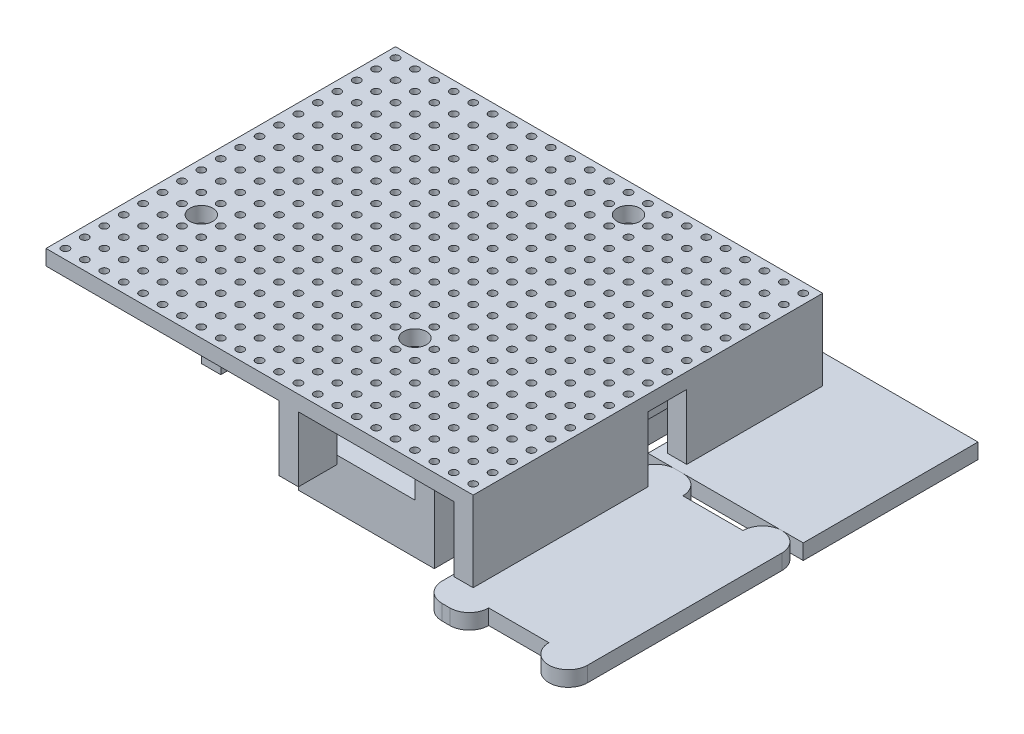
SolidWorks part; units mm, degrees
ref_plane "Front Plane" through (0, 0, 0) normal (0, 0, 1) x (1, 0, 0)
ref_plane "Top Plane" through (0, 0, 0) normal (0, 1, 0) x (1, 0, 0)
ref_plane "Right Plane" through (0, 0, 0) normal (1, 0, 0) x (0, 0, -1)
sketch "Sketch1" plane through (0, 0, 0) normal (0, 1, 0) x (1, 0, 0)
  line L1 (-28.6326, 15.7481) -> (34.8674, 15.7481)
  line L2 (-28.6326, 15.7481) -> (-28.6326, -29.9719)
  line L3 (-28.6326, -29.9719) -> (34.8674, -29.9719)
  line L4 (34.8674, 15.7481) -> (34.8674, -29.9719)
  circle A0 centre (33.5974, -28.7019) radius 0.5
  circle A1 centre (31.0574, -28.7019) radius 0.5
  circle A2 centre (28.5174, -28.7019) radius 0.5
  circle A3 centre (25.9774, -28.7019) radius 0.5
  circle A4 centre (23.4374, -28.7019) radius 0.5
  circle A5 centre (20.8974, -28.7019) radius 0.5
  circle A6 centre (18.3574, -28.7019) radius 0.5
  circle A7 centre (15.8174, -28.7019) radius 0.5
  circle A8 centre (13.2774, -28.7019) radius 0.5
  circle A9 centre (10.7374, -28.7019) radius 0.5
  circle A10 centre (8.1974, -28.7019) radius 0.5
  circle A11 centre (5.6574, -28.7019) radius 0.5
  circle A12 centre (3.1174, -28.7019) radius 0.5
  circle A13 centre (0.5774, -28.7019) radius 0.5
  circle A14 centre (-1.9626, -28.7019) radius 0.5
  circle A15 centre (-4.5026, -28.7019) radius 0.5
  circle A16 centre (-7.0426, -28.7019) radius 0.5
  circle A17 centre (-9.5826, -28.7019) radius 0.5
  circle A18 centre (-12.1226, -28.7019) radius 0.5
  circle A19 centre (-14.6626, -28.7019) radius 0.5
  circle A20 centre (-17.2026, -28.7019) radius 0.5
  circle A21 centre (-19.7426, -28.7019) radius 0.5
  circle A22 centre (-22.2826, -28.7019) radius 0.5
  circle A23 centre (-24.8226, -28.7019) radius 0.5
  circle A24 centre (-27.3626, -28.7019) radius 0.5
  circle A25 centre (31.0574, -26.1619) radius 0.5
  circle A26 centre (28.5174, -26.1619) radius 0.5
  circle A27 centre (25.9774, -26.1619) radius 0.5
  circle A28 centre (23.4374, -26.1619) radius 0.5
  circle A29 centre (20.8974, -26.1619) radius 0.5
  circle A30 centre (18.3574, -26.1619) radius 0.5
  circle A31 centre (15.8174, -26.1619) radius 0.5
  circle A32 centre (13.2774, -26.1619) radius 0.5
  circle A33 centre (10.7374, -26.1619) radius 0.5
  circle A34 centre (8.1974, -26.1619) radius 0.5
  circle A35 centre (5.6574, -26.1619) radius 0.5
  circle A36 centre (3.1174, -26.1619) radius 0.5
  circle A37 centre (0.5774, -26.1619) radius 0.5
  circle A38 centre (-1.9626, -26.1619) radius 0.5
  circle A39 centre (-4.5026, -26.1619) radius 0.5
  circle A40 centre (-7.0426, -26.1619) radius 0.5
  circle A41 centre (-9.5826, -26.1619) radius 0.5
  circle A42 centre (-12.1226, -26.1619) radius 0.5
  circle A43 centre (-14.6626, -26.1619) radius 0.5
  circle A44 centre (-17.2026, -26.1619) radius 0.5
  circle A45 centre (-19.7426, -26.1619) radius 0.5
  circle A46 centre (-22.2826, -26.1619) radius 0.5
  circle A47 centre (-24.8226, -26.1619) radius 0.5
  circle A48 centre (-27.3626, -26.1619) radius 0.5
  circle A49 centre (31.0574, -23.6219) radius 0.5
  circle A50 centre (28.5174, -23.6219) radius 0.5
  circle A51 centre (25.9774, -23.6219) radius 0.5
  circle A52 centre (23.4374, -23.6219) radius 0.5
  circle A53 centre (20.8974, -23.6219) radius 0.5
  circle A54 centre (18.3574, -23.6219) radius 0.5
  circle A55 centre (15.8174, -23.6219) radius 0.5
  circle A56 centre (13.2774, -23.6219) radius 0.5
  circle A57 centre (10.7374, -23.6219) radius 0.5
  circle A58 centre (8.1974, -23.6219) radius 0.5
  circle A59 centre (5.6574, -23.6219) radius 0.5
  circle A60 centre (3.1174, -23.6219) radius 0.5
  circle A61 centre (0.5774, -23.6219) radius 0.5
  circle A62 centre (-1.9626, -23.6219) radius 0.5
  circle A63 centre (-4.5026, -23.6219) radius 0.5
  circle A64 centre (-7.0426, -23.6219) radius 0.5
  circle A65 centre (-9.5826, -23.6219) radius 0.5
  circle A66 centre (-12.1226, -23.6219) radius 0.5
  circle A67 centre (-14.6626, -23.6219) radius 0.5
  circle A68 centre (-17.2026, -23.6219) radius 0.5
  circle A69 centre (-19.7426, -23.6219) radius 0.5
  circle A70 centre (-22.2826, -23.6219) radius 0.5
  circle A71 centre (-24.8226, -23.6219) radius 0.5
  circle A72 centre (-27.3626, -23.6219) radius 0.5
  circle A73 centre (31.0574, -21.0819) radius 0.5
  circle A74 centre (28.5174, -21.0819) radius 0.5
  circle A75 centre (25.9774, -21.0819) radius 0.5
  circle A76 centre (23.4374, -21.0819) radius 0.5
  circle A77 centre (20.8974, -21.0819) radius 0.5
  circle A78 centre (18.3574, -21.0819) radius 0.5
  circle A79 centre (15.8174, -21.0819) radius 0.5
  circle A80 centre (13.2774, -21.0819) radius 0.5
  circle A81 centre (10.7374, -21.0819) radius 0.5
  circle A82 centre (8.1974, -21.0819) radius 0.5
  circle A83 centre (5.6574, -21.0819) radius 0.5
  circle A84 centre (3.1174, -21.0819) radius 0.5
  circle A85 centre (0.5774, -21.0819) radius 0.5
  circle A86 centre (-1.9626, -21.0819) radius 0.5
  circle A87 centre (-4.5026, -21.0819) radius 0.5
  circle A88 centre (-7.0426, -21.0819) radius 0.5
  circle A89 centre (-9.5826, -21.0819) radius 0.5
  circle A90 centre (-12.1226, -21.0819) radius 0.5
  circle A91 centre (-14.6626, -21.0819) radius 0.5
  circle A92 centre (-17.2026, -21.0819) radius 0.5
  circle A93 centre (-19.7426, -21.0819) radius 0.5
  circle A94 centre (-22.2826, -21.0819) radius 0.5
  circle A95 centre (-24.8226, -21.0819) radius 0.5
  circle A96 centre (-27.3626, -21.0819) radius 0.5
  circle A97 centre (31.0574, -18.5419) radius 0.5
  circle A98 centre (28.5174, -18.5419) radius 0.5
  circle A99 centre (25.9774, -18.5419) radius 0.5
  circle A100 centre (23.4374, -18.5419) radius 0.5
  circle A101 centre (20.8974, -18.5419) radius 0.5
  circle A102 centre (18.3574, -18.5419) radius 0.5
  circle A103 centre (15.8174, -18.5419) radius 0.5
  circle A104 centre (13.2774, -18.5419) radius 0.5
  circle A105 centre (10.7374, -18.5419) radius 0.5
  circle A106 centre (8.1974, -18.5419) radius 0.5
  circle A107 centre (5.6574, -18.5419) radius 0.5
  circle A108 centre (3.1174, -18.5419) radius 0.5
  circle A109 centre (0.5774, -18.5419) radius 0.5
  circle A110 centre (-1.9626, -18.5419) radius 0.5
  circle A111 centre (-4.5026, -18.5419) radius 0.5
  circle A112 centre (-7.0426, -18.5419) radius 0.5
  circle A113 centre (-9.5826, -18.5419) radius 0.5
  circle A114 centre (-12.1226, -18.5419) radius 0.5
  circle A115 centre (-14.6626, -18.5419) radius 0.5
  circle A116 centre (-17.2026, -18.5419) radius 0.5
  circle A117 centre (-19.7426, -18.5419) radius 0.5
  circle A118 centre (-22.2826, -18.5419) radius 0.5
  circle A119 centre (-24.8226, -18.5419) radius 0.5
  circle A120 centre (-27.3626, -18.5419) radius 0.5
  circle A121 centre (31.0574, -16.0019) radius 0.5
  circle A122 centre (28.5174, -16.0019) radius 0.5
  circle A123 centre (25.9774, -16.0019) radius 0.5
  circle A124 centre (23.4374, -16.0019) radius 0.5
  circle A125 centre (20.8974, -16.0019) radius 0.5
  circle A126 centre (18.3574, -16.0019) radius 0.5
  circle A127 centre (15.8174, -16.0019) radius 0.5
  circle A128 centre (13.2774, -16.0019) radius 0.5
  circle A129 centre (10.7374, -16.0019) radius 0.5
  circle A130 centre (8.1974, -16.0019) radius 0.5
  circle A131 centre (5.6574, -16.0019) radius 0.5
  circle A132 centre (3.1174, -16.0019) radius 0.5
  circle A133 centre (0.5774, -16.0019) radius 0.5
  circle A134 centre (-1.9626, -16.0019) radius 0.5
  circle A135 centre (-4.5026, -16.0019) radius 0.5
  circle A136 centre (-7.0426, -16.0019) radius 0.5
  circle A137 centre (-9.5826, -16.0019) radius 0.5
  circle A138 centre (-12.1226, -16.0019) radius 0.5
  circle A139 centre (-14.6626, -16.0019) radius 0.5
  circle A140 centre (-17.2026, -16.0019) radius 0.5
  circle A141 centre (-19.7426, -16.0019) radius 0.5
  circle A142 centre (-22.2826, -16.0019) radius 0.5
  circle A143 centre (-24.8226, -16.0019) radius 0.5
  circle A144 centre (-27.3626, -16.0019) radius 0.5
  circle A145 centre (31.0574, -13.4619) radius 0.5
  circle A146 centre (28.5174, -13.4619) radius 0.5
  circle A147 centre (25.9774, -13.4619) radius 0.5
  circle A148 centre (23.4374, -13.4619) radius 0.5
  circle A149 centre (20.8974, -13.4619) radius 0.5
  circle A150 centre (18.3574, -13.4619) radius 0.5
  circle A151 centre (15.8174, -13.4619) radius 0.5
  circle A152 centre (13.2774, -13.4619) radius 0.5
  circle A153 centre (10.7374, -13.4619) radius 0.5
  circle A154 centre (8.1974, -13.4619) radius 0.5
  circle A155 centre (5.6574, -13.4619) radius 0.5
  circle A156 centre (3.1174, -13.4619) radius 0.5
  circle A157 centre (0.5774, -13.4619) radius 0.5
  circle A158 centre (-1.9626, -13.4619) radius 0.5
  circle A159 centre (-4.5026, -13.4619) radius 0.5
  circle A160 centre (-7.0426, -13.4619) radius 0.5
  circle A161 centre (-9.5826, -13.4619) radius 0.5
  circle A162 centre (-12.1226, -13.4619) radius 0.5
  circle A163 centre (-14.6626, -13.4619) radius 0.5
  circle A164 centre (-17.2026, -13.4619) radius 0.5
  circle A165 centre (-19.7426, -13.4619) radius 0.5
  circle A166 centre (-22.2826, -13.4619) radius 0.5
  circle A167 centre (-24.8226, -13.4619) radius 0.5
  circle A168 centre (-27.3626, -13.4619) radius 0.5
  circle A169 centre (31.0574, -10.9219) radius 0.5
  circle A170 centre (28.5174, -10.9219) radius 0.5
  circle A171 centre (25.9774, -10.9219) radius 0.5
  circle A172 centre (23.4374, -10.9219) radius 0.5
  circle A173 centre (20.8974, -10.9219) radius 0.5
  circle A174 centre (18.3574, -10.9219) radius 0.5
  circle A175 centre (15.8174, -10.9219) radius 0.5
  circle A176 centre (13.2774, -10.9219) radius 0.5
  circle A177 centre (10.7374, -10.9219) radius 0.5
  circle A178 centre (8.1974, -10.9219) radius 0.5
  circle A179 centre (5.6574, -10.9219) radius 0.5
  circle A180 centre (3.1174, -10.9219) radius 0.5
  circle A181 centre (0.5774, -10.9219) radius 0.5
  circle A182 centre (-1.9626, -10.9219) radius 0.5
  circle A183 centre (-4.5026, -10.9219) radius 0.5
  circle A184 centre (-7.0426, -10.9219) radius 0.5
  circle A185 centre (-9.5826, -10.9219) radius 0.5
  circle A186 centre (-12.1226, -10.9219) radius 0.5
  circle A187 centre (-14.6626, -10.9219) radius 0.5
  circle A188 centre (-17.2026, -10.9219) radius 0.5
  circle A189 centre (-19.7426, -10.9219) radius 0.5
  circle A190 centre (-22.2826, -10.9219) radius 0.5
  circle A191 centre (-24.8226, -10.9219) radius 0.5
  circle A192 centre (-27.3626, -10.9219) radius 0.5
  circle A193 centre (31.0574, -8.3819) radius 0.5
  circle A194 centre (28.5174, -8.3819) radius 0.5
  circle A195 centre (25.9774, -8.3819) radius 0.5
  circle A196 centre (23.4374, -8.3819) radius 0.5
  circle A197 centre (20.8974, -8.3819) radius 0.5
  circle A198 centre (18.3574, -8.3819) radius 0.5
  circle A199 centre (15.8174, -8.3819) radius 0.5
  circle A200 centre (13.2774, -8.3819) radius 0.5
  circle A201 centre (10.7374, -8.3819) radius 0.5
  circle A202 centre (8.1974, -8.3819) radius 0.5
  circle A203 centre (5.6574, -8.3819) radius 0.5
  circle A204 centre (3.1174, -8.3819) radius 0.5
  circle A205 centre (0.5774, -8.3819) radius 0.5
  circle A206 centre (-1.9626, -8.3819) radius 0.5
  circle A207 centre (-4.5026, -8.3819) radius 0.5
  circle A208 centre (-7.0426, -8.3819) radius 0.5
  circle A209 centre (-9.5826, -8.3819) radius 0.5
  circle A210 centre (-12.1226, -8.3819) radius 0.5
  circle A211 centre (-14.6626, -8.3819) radius 0.5
  circle A212 centre (-17.2026, -8.3819) radius 0.5
  circle A213 centre (-19.7426, -8.3819) radius 0.5
  circle A214 centre (-22.2826, -8.3819) radius 0.5
  circle A215 centre (-24.8226, -8.3819) radius 0.5
  circle A216 centre (-27.3626, -8.3819) radius 0.5
  circle A217 centre (31.0574, -5.8419) radius 0.5
  circle A218 centre (28.5174, -5.8419) radius 0.5
  circle A219 centre (25.9774, -5.8419) radius 0.5
  circle A220 centre (23.4374, -5.8419) radius 0.5
  circle A221 centre (20.8974, -5.8419) radius 0.5
  circle A222 centre (18.3574, -5.8419) radius 0.5
  circle A223 centre (15.8174, -5.8419) radius 0.5
  circle A224 centre (13.2774, -5.8419) radius 0.5
  circle A225 centre (10.7374, -5.8419) radius 0.5
  circle A226 centre (8.1974, -5.8419) radius 0.5
  circle A227 centre (5.6574, -5.8419) radius 0.5
  circle A228 centre (3.1174, -5.8419) radius 0.5
  circle A229 centre (0.5774, -5.8419) radius 0.5
  circle A230 centre (-1.9626, -5.8419) radius 0.5
  circle A231 centre (-4.5026, -5.8419) radius 0.5
  circle A232 centre (-7.0426, -5.8419) radius 0.5
  circle A233 centre (-9.5826, -5.8419) radius 0.5
  circle A234 centre (-12.1226, -5.8419) radius 0.5
  circle A235 centre (-14.6626, -5.8419) radius 0.5
  circle A236 centre (-17.2026, -5.8419) radius 0.5
  circle A237 centre (-19.7426, -5.8419) radius 0.5
  circle A238 centre (-22.2826, -5.8419) radius 0.5
  circle A239 centre (-24.8226, -5.8419) radius 0.5
  circle A240 centre (-27.3626, -5.8419) radius 0.5
  circle A241 centre (31.0574, -3.3019) radius 0.5
  circle A242 centre (28.5174, -3.3019) radius 0.5
  circle A243 centre (25.9774, -3.3019) radius 0.5
  circle A244 centre (23.4374, -3.3019) radius 0.5
  circle A245 centre (20.8974, -3.3019) radius 0.5
  circle A246 centre (18.3574, -3.3019) radius 0.5
  circle A247 centre (15.8174, -3.3019) radius 0.5
  circle A248 centre (13.2774, -3.3019) radius 0.5
  circle A249 centre (10.7374, -3.3019) radius 0.5
  circle A250 centre (8.1974, -3.3019) radius 0.5
  circle A251 centre (5.6574, -3.3019) radius 0.5
  circle A252 centre (3.1174, -3.3019) radius 0.5
  circle A253 centre (0.5774, -3.3019) radius 0.5
  circle A254 centre (-1.9626, -3.3019) radius 0.5
  circle A255 centre (-4.5026, -3.3019) radius 0.5
  circle A256 centre (-7.0426, -3.3019) radius 0.5
  circle A257 centre (-9.5826, -3.3019) radius 0.5
  circle A258 centre (-12.1226, -3.3019) radius 0.5
  circle A259 centre (-14.6626, -3.3019) radius 0.5
  circle A260 centre (-17.2026, -3.3019) radius 0.5
  circle A261 centre (-19.7426, -3.3019) radius 0.5
  circle A262 centre (-22.2826, -3.3019) radius 0.5
  circle A263 centre (-24.8226, -3.3019) radius 0.5
  circle A264 centre (-27.3626, -3.3019) radius 0.5
  circle A265 centre (31.0574, -0.7619) radius 0.5
  circle A266 centre (28.5174, -0.7619) radius 0.5
  circle A267 centre (25.9774, -0.7619) radius 0.5
  circle A268 centre (23.4374, -0.7619) radius 0.5
  circle A269 centre (20.8974, -0.7619) radius 0.5
  circle A270 centre (18.3574, -0.7619) radius 0.5
  circle A271 centre (15.8174, -0.7619) radius 0.5
  circle A272 centre (13.2774, -0.7619) radius 0.5
  circle A273 centre (10.7374, -0.7619) radius 0.5
  circle A274 centre (8.1974, -0.7619) radius 0.5
  circle A275 centre (5.6574, -0.7619) radius 0.5
  circle A276 centre (3.1174, -0.7619) radius 0.5
  circle A277 centre (0.5774, -0.7619) radius 0.5
  circle A278 centre (-1.9626, -0.7619) radius 0.5
  circle A279 centre (-4.5026, -0.7619) radius 0.5
  circle A280 centre (-7.0426, -0.7619) radius 0.5
  circle A281 centre (-9.5826, -0.7619) radius 0.5
  circle A282 centre (-12.1226, -0.7619) radius 0.5
  circle A283 centre (-14.6626, -0.7619) radius 0.5
  circle A284 centre (-17.2026, -0.7619) radius 0.5
  circle A285 centre (-19.7426, -0.7619) radius 0.5
  circle A286 centre (-22.2826, -0.7619) radius 0.5
  circle A287 centre (-24.8226, -0.7619) radius 0.5
  circle A288 centre (-27.3626, -0.7619) radius 0.5
  circle A289 centre (31.0574, 1.7781) radius 0.5
  circle A290 centre (28.5174, 1.7781) radius 0.5
  circle A291 centre (25.9774, 1.7781) radius 0.5
  circle A292 centre (23.4374, 1.7781) radius 0.5
  circle A293 centre (20.8974, 1.7781) radius 0.5
  circle A294 centre (18.3574, 1.7781) radius 0.5
  circle A295 centre (15.8174, 1.7781) radius 0.5
  circle A296 centre (13.2774, 1.7781) radius 0.5
  circle A297 centre (10.7374, 1.7781) radius 0.5
  circle A298 centre (8.1974, 1.7781) radius 0.5
  circle A299 centre (5.6574, 1.7781) radius 0.5
  circle A300 centre (3.1174, 1.7781) radius 0.5
  circle A301 centre (0.5774, 1.7781) radius 0.5
  circle A302 centre (-1.9626, 1.7781) radius 0.5
  circle A303 centre (-4.5026, 1.7781) radius 0.5
  circle A304 centre (-7.0426, 1.7781) radius 0.5
  circle A305 centre (-9.5826, 1.7781) radius 0.5
  circle A306 centre (-12.1226, 1.7781) radius 0.5
  circle A307 centre (-14.6626, 1.7781) radius 0.5
  circle A308 centre (-17.2026, 1.7781) radius 0.5
  circle A309 centre (-19.7426, 1.7781) radius 0.5
  circle A310 centre (-22.2826, 1.7781) radius 0.5
  circle A311 centre (-24.8226, 1.7781) radius 0.5
  circle A312 centre (-27.3626, 1.7781) radius 0.5
  circle A313 centre (31.0574, 4.3181) radius 0.5
  circle A314 centre (28.5174, 4.3181) radius 0.5
  circle A315 centre (25.9774, 4.3181) radius 0.5
  circle A316 centre (23.4374, 4.3181) radius 0.5
  circle A317 centre (20.8974, 4.3181) radius 0.5
  circle A318 centre (18.3574, 4.3181) radius 0.5
  circle A319 centre (15.8174, 4.3181) radius 0.5
  circle A320 centre (13.2774, 4.3181) radius 0.5
  circle A321 centre (10.7374, 4.3181) radius 0.5
  circle A322 centre (8.1974, 4.3181) radius 0.5
  circle A323 centre (5.6574, 4.3181) radius 0.5
  circle A324 centre (3.1174, 4.3181) radius 0.5
  circle A325 centre (0.5774, 4.3181) radius 0.5
  circle A326 centre (-1.9626, 4.3181) radius 0.5
  circle A327 centre (-4.5026, 4.3181) radius 0.5
  circle A328 centre (-7.0426, 4.3181) radius 0.5
  circle A329 centre (-9.5826, 4.3181) radius 0.5
  circle A330 centre (-12.1226, 4.3181) radius 0.5
  circle A331 centre (-14.6626, 4.3181) radius 0.5
  circle A332 centre (-17.2026, 4.3181) radius 0.5
  circle A333 centre (-19.7426, 4.3181) radius 0.5
  circle A334 centre (-22.2826, 4.3181) radius 0.5
  circle A335 centre (-24.8226, 4.3181) radius 0.5
  circle A336 centre (-27.3626, 4.3181) radius 0.5
  circle A337 centre (31.0574, 6.8581) radius 0.5
  circle A338 centre (28.5174, 6.8581) radius 0.5
  circle A339 centre (25.9774, 6.8581) radius 0.5
  circle A340 centre (23.4374, 6.8581) radius 0.5
  circle A341 centre (20.8974, 6.8581) radius 0.5
  circle A342 centre (18.3574, 6.8581) radius 0.5
  circle A343 centre (15.8174, 6.8581) radius 0.5
  circle A344 centre (13.2774, 6.8581) radius 0.5
  circle A345 centre (10.7374, 6.8581) radius 0.5
  circle A346 centre (8.1974, 6.8581) radius 0.5
  circle A347 centre (5.6574, 6.8581) radius 0.5
  circle A348 centre (3.1174, 6.8581) radius 0.5
  circle A349 centre (0.5774, 6.8581) radius 0.5
  circle A350 centre (-1.9626, 6.8581) radius 0.5
  circle A351 centre (-4.5026, 6.8581) radius 0.5
  circle A352 centre (-7.0426, 6.8581) radius 0.5
  circle A353 centre (-9.5826, 6.8581) radius 0.5
  circle A354 centre (-12.1226, 6.8581) radius 0.5
  circle A355 centre (-14.6626, 6.8581) radius 0.5
  circle A356 centre (-17.2026, 6.8581) radius 0.5
  circle A357 centre (-19.7426, 6.8581) radius 0.5
  circle A358 centre (-22.2826, 6.8581) radius 0.5
  circle A359 centre (-24.8226, 6.8581) radius 0.5
  circle A360 centre (-27.3626, 6.8581) radius 0.5
  circle A361 centre (31.0574, 9.3981) radius 0.5
  circle A362 centre (28.5174, 9.3981) radius 0.5
  circle A363 centre (25.9774, 9.3981) radius 0.5
  circle A364 centre (23.4374, 9.3981) radius 0.5
  circle A365 centre (20.8974, 9.3981) radius 0.5
  circle A366 centre (18.3574, 9.3981) radius 0.5
  circle A367 centre (15.8174, 9.3981) radius 0.5
  circle A368 centre (13.2774, 9.3981) radius 0.5
  circle A369 centre (10.7374, 9.3981) radius 0.5
  circle A370 centre (8.1974, 9.3981) radius 0.5
  circle A371 centre (5.6574, 9.3981) radius 0.5
  circle A372 centre (3.1174, 9.3981) radius 0.5
  circle A373 centre (0.5774, 9.3981) radius 0.5
  circle A374 centre (-1.9626, 9.3981) radius 0.5
  circle A375 centre (-4.5026, 9.3981) radius 0.5
  circle A376 centre (-7.0426, 9.3981) radius 0.5
  circle A377 centre (-9.5826, 9.3981) radius 0.5
  circle A378 centre (-12.1226, 9.3981) radius 0.5
  circle A379 centre (-14.6626, 9.3981) radius 0.5
  circle A380 centre (-17.2026, 9.3981) radius 0.5
  circle A381 centre (-19.7426, 9.3981) radius 0.5
  circle A382 centre (-22.2826, 9.3981) radius 0.5
  circle A383 centre (-24.8226, 9.3981) radius 0.5
  circle A384 centre (-27.3626, 9.3981) radius 0.5
  circle A385 centre (31.0574, 11.9381) radius 0.5
  circle A386 centre (28.5174, 11.9381) radius 0.5
  circle A387 centre (25.9774, 11.9381) radius 0.5
  circle A388 centre (23.4374, 11.9381) radius 0.5
  circle A389 centre (20.8974, 11.9381) radius 0.5
  circle A390 centre (18.3574, 11.9381) radius 0.5
  circle A391 centre (15.8174, 11.9381) radius 0.5
  circle A392 centre (13.2774, 11.9381) radius 0.5
  circle A393 centre (10.7374, 11.9381) radius 0.5
  circle A394 centre (8.1974, 11.9381) radius 0.5
  circle A395 centre (5.6574, 11.9381) radius 0.5
  circle A396 centre (3.1174, 11.9381) radius 0.5
  circle A397 centre (0.5774, 11.9381) radius 0.5
  circle A398 centre (-1.9626, 11.9381) radius 0.5
  circle A399 centre (-4.5026, 11.9381) radius 0.5
  circle A400 centre (-7.0426, 11.9381) radius 0.5
  circle A401 centre (-9.5826, 11.9381) radius 0.5
  circle A402 centre (-12.1226, 11.9381) radius 0.5
  circle A403 centre (-14.6626, 11.9381) radius 0.5
  circle A404 centre (-17.2026, 11.9381) radius 0.5
  circle A405 centre (-19.7426, 11.9381) radius 0.5
  circle A406 centre (-22.2826, 11.9381) radius 0.5
  circle A407 centre (-24.8226, 11.9381) radius 0.5
  circle A408 centre (-27.3626, 11.9381) radius 0.5
  circle A409 centre (33.5974, -26.1619) radius 0.5
  circle A410 centre (33.5974, -23.6219) radius 0.5
  circle A411 centre (33.5974, -21.0819) radius 0.5
  circle A412 centre (33.5974, -18.5419) radius 0.5
  circle A413 centre (33.5974, -16.0019) radius 0.5
  circle A414 centre (33.5974, -13.4619) radius 0.5
  circle A415 centre (33.5974, -10.9219) radius 0.5
  circle A416 centre (33.5974, -8.3819) radius 0.5
  circle A417 centre (33.5974, -5.8419) radius 0.5
  circle A418 centre (33.5974, -3.3019) radius 0.5
  circle A419 centre (33.5974, -0.7619) radius 0.5
  circle A420 centre (33.5974, 1.7781) radius 0.5
  circle A421 centre (33.5974, 4.3181) radius 0.5
  circle A422 centre (33.5974, 6.8581) radius 0.5
  circle A423 centre (33.5974, 9.3981) radius 0.5
  circle A424 centre (33.5974, 11.9381) radius 0.5
  circle A425 centre (33.5974, 14.4781) radius 0.5
  circle A426 centre (31.0574, 14.4781) radius 0.5
  circle A427 centre (28.5174, 14.4781) radius 0.5
  circle A428 centre (25.9774, 14.4781) radius 0.5
  circle A429 centre (23.4374, 14.4781) radius 0.5
  circle A430 centre (20.8974, 14.4781) radius 0.5
  circle A431 centre (18.3574, 14.4781) radius 0.5
  circle A432 centre (15.8174, 14.4781) radius 0.5
  circle A433 centre (13.2774, 14.4781) radius 0.5
  circle A434 centre (10.7374, 14.4781) radius 0.5
  circle A435 centre (8.1974, 14.4781) radius 0.5
  circle A436 centre (5.6574, 14.4781) radius 0.5
  circle A437 centre (3.1174, 14.4781) radius 0.5
  circle A438 centre (0.5774, 14.4781) radius 0.5
  circle A439 centre (-1.9626, 14.4781) radius 0.5
  circle A440 centre (-4.5026, 14.4781) radius 0.5
  circle A441 centre (-7.0426, 14.4781) radius 0.5
  circle A442 centre (-9.5826, 14.4781) radius 0.5
  circle A443 centre (-12.1226, 14.4781) radius 0.5
  circle A444 centre (-14.6626, 14.4781) radius 0.5
  circle A445 centre (-17.2026, 14.4781) radius 0.5
  circle A446 centre (-19.7426, 14.4781) radius 0.5
  circle A447 centre (-22.2826, 14.4781) radius 0.5
  circle A448 centre (-24.8226, 14.4781) radius 0.5
  circle A449 centre (-27.3626, 14.4781) radius 0.5
  dimension "D3" = 1
  dimension "D1" = 45.72
  dimension "D2" = 63.5
  dimension "D6" = 1.27
  dimension "D7" = 1.27
  dimension "D4" = 25
  dimension "D5" = 18
extrude "Boss-Extrude1" add sketch "Sketch1" along normal blind 2
sketch "Sketch2" plane through (0, 0, 0) normal (0, -1, 0) x (-1, 0, 0)
  line L0 (-34.8674, 15.7481) -> (28.6326, 15.7481) construction
  line L1 (3.2326, -22.3519) -> (-14.5474, -22.3519)
  line L2 (3.2326, -22.3519) -> (3.2326, 15.7481)
  line L3 (3.2326, 15.7481) -> (-14.5474, 15.7481)
  line L4 (-14.5474, -22.3519) -> (-14.5474, 15.7481)
  line L5 (28.6326, 15.7481) -> (28.6326, -29.9719) construction
  dimension "D1" = 25.4
  dimension "D2" = 17.78
  dimension "D3" = 38.1
extrude "Arduino Nano" add sketch "Sketch2" along normal blind 16.5
sketch "Sketch6" plane through (0, 0, -15.7481) normal (0, 0, -1) x (-1, 0, 0)
  line L0 (-14.5474, -16.5) -> (-14.5474, 0) construction
  line L1 (0.7326, 0) -> (-12.0474, 0)
  line L2 (0.7326, 0) -> (0.7326, -10)
  line L3 (0.7326, -10) -> (-12.0474, -10)
  line L4 (-12.0474, 0) -> (-12.0474, -10)
  line L5 (3.2326, -16.5) -> (3.2326, 0) construction
  line L6 (3.2326, 0) -> (28.6326, 0) construction
  dimension "D1" = 10
  dimension "D2" = 2.5
  dimension "D3" = 2.5
extrude "Cut-Extrude2" cut sketch "Sketch6" against normal through all both and the other way through all
sketch "Sketch3" plane through (0, 0, 0) normal (0, -1, 0) x (-1, 0, 0)
  line L1 (28.6326, 15.7481) -> (18.4726, 15.7481)
  line L2 (28.6326, 15.7481) -> (28.6326, -4.5719)
  line L3 (28.6326, -4.5719) -> (18.4726, -4.5719)
  line L4 (18.4726, 15.7481) -> (18.4726, -4.5719)
  dimension "D1" = 20.32
  dimension "D2" = 10.16
extrude "Relay" add sketch "Sketch3" along normal blind 11
sketch "Sketch4" plane through (0, 0, 0) normal (0, -1, 0) x (-1, 0, 0)
  line L0 (3.2326, 15.7481) -> (18.4726, 15.7481) construction
  line L1 (15.9326, 10.6681) -> (13.3926, 10.6681)
  line L2 (15.9326, 10.6681) -> (15.9326, 15.7481)
  line L3 (15.9326, 15.7481) -> (13.3926, 15.7481)
  line L4 (13.3926, 10.6681) -> (13.3926, 15.7481)
  line L5 (18.4726, 15.7481) -> (18.4726, -4.5719) construction
  line L6 (-34.8674, 15.7481) -> (-14.5474, 15.7481) construction
  line L7 (13.3926, 8.1281) -> (15.9326, 8.1281)
  line L8 (13.3926, 8.1281) -> (13.3926, -2.0319)
  line L9 (13.3926, -2.0319) -> (15.9326, -2.0319)
  line L10 (15.9326, 8.1281) -> (15.9326, -2.0319)
  line L11 (13.3926, -4.5719) -> (15.9326, -4.5719)
  line L12 (13.3926, -4.5719) -> (13.3926, -22.3519)
  line L13 (13.3926, -22.3519) -> (15.9326, -22.3519)
  line L14 (15.9326, -4.5719) -> (15.9326, -22.3519)
  line L15 (-19.6274, 8.1281) -> (-17.0874, 8.1281)
  line L16 (-19.6274, 8.1281) -> (-19.6274, 0.5081)
  line L17 (-19.6274, 0.5081) -> (-17.0874, 0.5081)
  line L18 (-17.0874, 8.1281) -> (-17.0874, 0.5081)
  line L19 (-14.5474, 15.7481) -> (-14.5474, -22.3519) construction
  line L20 (28.6326, -29.9719) -> (-34.8674, -29.9719) construction
  line L21 (-27.2474, 15.7481) -> (-24.7074, 15.7481)
  line L22 (-27.2474, 15.7481) -> (-27.2474, -2.0319)
  line L23 (-27.2474, -2.0319) -> (-24.7074, -2.0319)
  line L24 (-24.7074, 15.7481) -> (-24.7074, -2.0319)
  line L25 (-27.2474, -7.1119) -> (-24.7074, -7.1119)
  line L26 (-27.2474, -7.1119) -> (-27.2474, -29.9719)
  line L27 (-27.2474, -29.9719) -> (-24.7074, -29.9719)
  line L28 (-24.7074, -7.1119) -> (-24.7074, -29.9719)
  line L29 (3.2326, -22.3519) -> (3.2326, 15.7481) construction
  line L30 (-1.8474, -24.8919) -> (-4.3874, -24.8919)
  line L31 (-1.8474, -24.8919) -> (-1.8474, -29.9719)
  line L32 (-1.8474, -29.9719) -> (-4.3874, -29.9719)
  line L33 (-4.3874, -24.8919) -> (-4.3874, -29.9719)
  line L34 (5.7726, -4.5719) -> (3.2326, -4.5719)
  line L35 (5.7726, -4.5719) -> (5.7726, -7.1119)
  line L36 (5.7726, -7.1119) -> (3.2326, -7.1119)
  line L37 (3.2326, -4.5719) -> (3.2326, -7.1119)
  point P12 (14.6626, 8.1281)
  point P39 (-3.1174, -29.9719)
  point P41 (-3.1174, -29.9719)
  dimension "D1" = 2.54
  dimension "D2" = 5.08
  dimension "D3" = 2.54
  dimension "D4" = 10.16
  dimension "D5" = 2.54
  dimension "D6" = 2.54
  dimension "D7" = 17.78
  dimension "D8" = 2.54
  dimension "D9" = 7.62
  dimension "D10" = 2.54
  dimension "D11" = 7.62
  dimension "D12" = 2.54
  dimension "D13" = 17.78
  dimension "D14" = 2.54
  dimension "D15" = 5.08
  dimension "D16" = 22.86
  dimension "D17" = 5.08
  dimension "D18" = 2.54
  dimension "D19" = 2.54
  dimension "D20" = 2.54
extrude "Female Connectors" add sketch "Sketch4" along normal blind 8.5
sketch "Sketch5" plane through (0, 0, 0) normal (0, -1, 0) x (-1, 0, 0)
  circle A2 centre (22.2826, -16.0019) radius 1.5
  circle A3 centre (-5.6574, 11.9381) radius 1.5
  circle A4 centre (-5.6574, -16.0019) radius 1.5
  point P2 (0, 0)
  point P5 (22.2826, -16.0019)
  point P7 (22.2826, -16.0019)
  point P11 (0, 0)
  point P12 (-5.6574, -18.5419)
  point P16 (-5.6574, -18.5419)
  point P17 (-4.4388, -17.0266)
  point P18 (-5.6574, -16.0019)
  dimension "D1" = 3
extrude "Mounting Holes" cut sketch "Sketch5" against normal blind 8.5
sketch "Sketch7" plane through (0, -8.5, 0) normal (0, -1, 0) x (-1, 0, 0)
  line L1 (-23.4374, -3.3019) -> (-43.7574, -3.3019)
  line L2 (-23.4374, -3.3019) -> (-23.4374, 19.5581)
  line L3 (-23.4374, 19.5581) -> (-43.7574, 19.5581)
  line L4 (-43.7574, -3.3019) -> (-43.7574, 19.5581)
  line L5 (-27.2474, 15.7481) -> (-27.2474, -2.0319) construction
  line L7 (-27.2474, -2.0319) -> (-24.7074, -2.0319) construction
  dimension "D1" = 22.86
  dimension "D2" = 20.32
  dimension "D3" = 1.27
  dimension "D4" = 3.81
extrude "LSM303" add sketch "Sketch7" along normal blind 2
sketch "Sketch8" plane through (0, -8.5, 0) normal (0, -1, 0) x (1, 0, 0)
  line L0 (24.7074, 29.9719) -> (24.7074, 7.1119) construction
  line L1 (26.9934, 33.7819) -> (28.0094, 33.7819)
  line L2 (24.4534, 31.2419) -> (24.4534, 5.8419)
  line L3 (26.9934, 3.3019) -> (28.0094, 3.3019)
  line L4 (43.5034, 31.2419) -> (43.5034, 5.8419)
  line L9 (28.0094, 5.8419) -> (28.0094, 31.2419) construction
  line L10 (40.9634, 5.8419) -> (28.0094, 5.8419) construction
  line L11 (38.4234, 5.8419) -> (30.5494, 5.8419)
  line L12 (38.4234, 31.2419) -> (30.5494, 31.2419)
  arc A0 (38.4234, 5.8419) -> (43.5034, 5.8419) centre (40.9634, 5.8419) ccw
  arc A1 (43.5034, 31.2419) -> (38.4234, 31.2419) centre (40.9634, 31.2419) ccw
  arc A2 (30.5494, 31.2419) -> (28.0094, 33.7819) centre (28.0094, 31.2419) ccw
  arc A3 (28.0094, 3.3019) -> (30.5494, 5.8419) centre (28.0094, 5.8419) ccw
  arc A5 (26.9934, 33.7819) -> (24.4534, 31.2419) centre (26.9934, 31.2419) ccw
  arc A6 (26.9934, 3.3019) -> (24.4534, 5.8419) centre (26.9934, 5.8419) cw
  dimension "D4" = 5.08
  dimension "D5" = 5.08
  dimension "D7" = 5.08
  dimension "D8" = 5.08
  dimension "D9" = 2.54
  dimension "D10" = 2.54
  dimension "D1" = 19.05
  dimension "D2" = 0.254
  dimension "D3" = 30.48
  dimension "D6" = 3.556
extrude "Gyro" add sketch "Sketch8" along normal blind 2 separate body
sketch "Sketch9" plane through (0, 2, 0) normal (0, 1, 0) x (1, 0, 0)
  line L0 (34.8674, 15.7481) -> (-28.6326, 15.7481) construction
  line L1 (34.8674, -29.9719) -> (27.2474, -29.9719)
  line L2 (34.8674, -29.9719) -> (34.8674, 15.7481)
  line L3 (34.8674, 15.7481) -> (27.2474, 15.7481)
  line L4 (27.2474, -29.9719) -> (27.2474, 15.7481)
  dimension "D1" = 7.62
extrude "Cut-Extrude3" cut sketch "Sketch9" against normal blind 3
